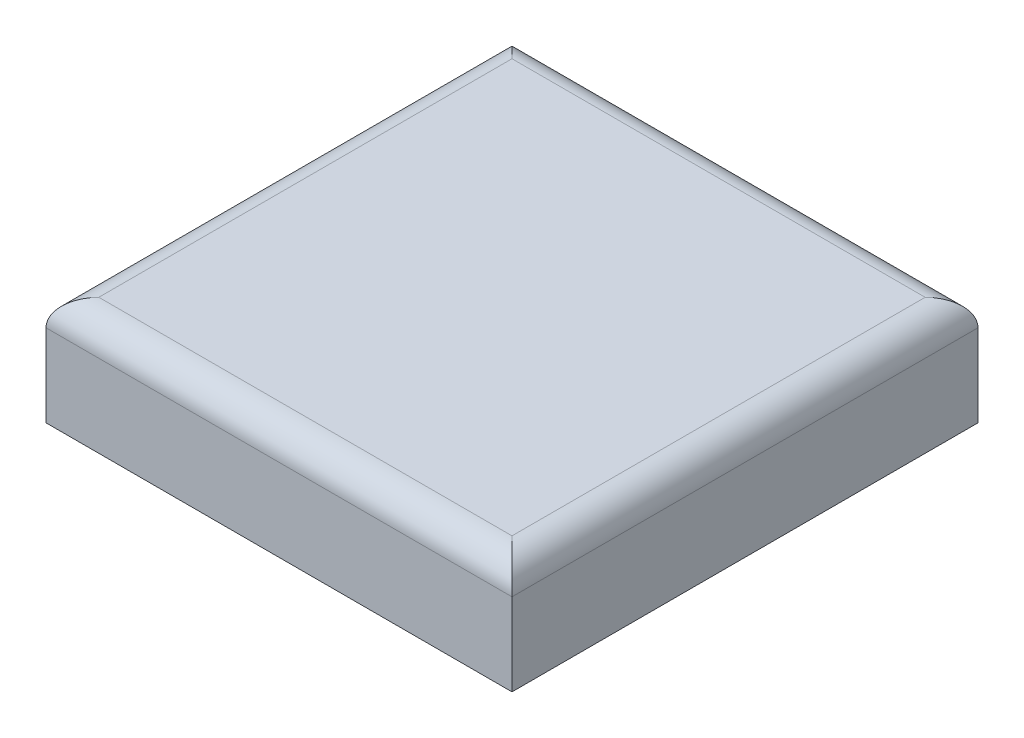
SolidWorks part; units mm, degrees
ref_plane "Alzado" through (0, 0, 0) normal (0, 0, 1) x (1, 0, 0)
ref_plane "Planta" through (0, 0, 0) normal (0, 1, 0) x (1, 0, 0)
ref_plane "Vista lateral" through (0, 0, 0) normal (1, 0, 0) x (0, 0, -1)
sketch "Croquis1" plane through (0, 0, 0) normal (0, 1, 0) x (1, 0, 0)
  line L1 (0, 0) -> (3000, 0)
  line L2 (0, 0) -> (0, 3000)
  line L3 (0, 3000) -> (3000, 3000)
  line L4 (3000, 0) -> (3000, 3000)
  dimension "D1" = 3000
  dimension "D2" = 3000
extrude "Saliente-Extruir1" add sketch "Croquis1" along normal blind 700
fillet "Redondeo1" radius 170 4 edges at (0, 700, -1500) (1500, 700, -3000) (3000, 700, -1500) (1500, 700, 0)
